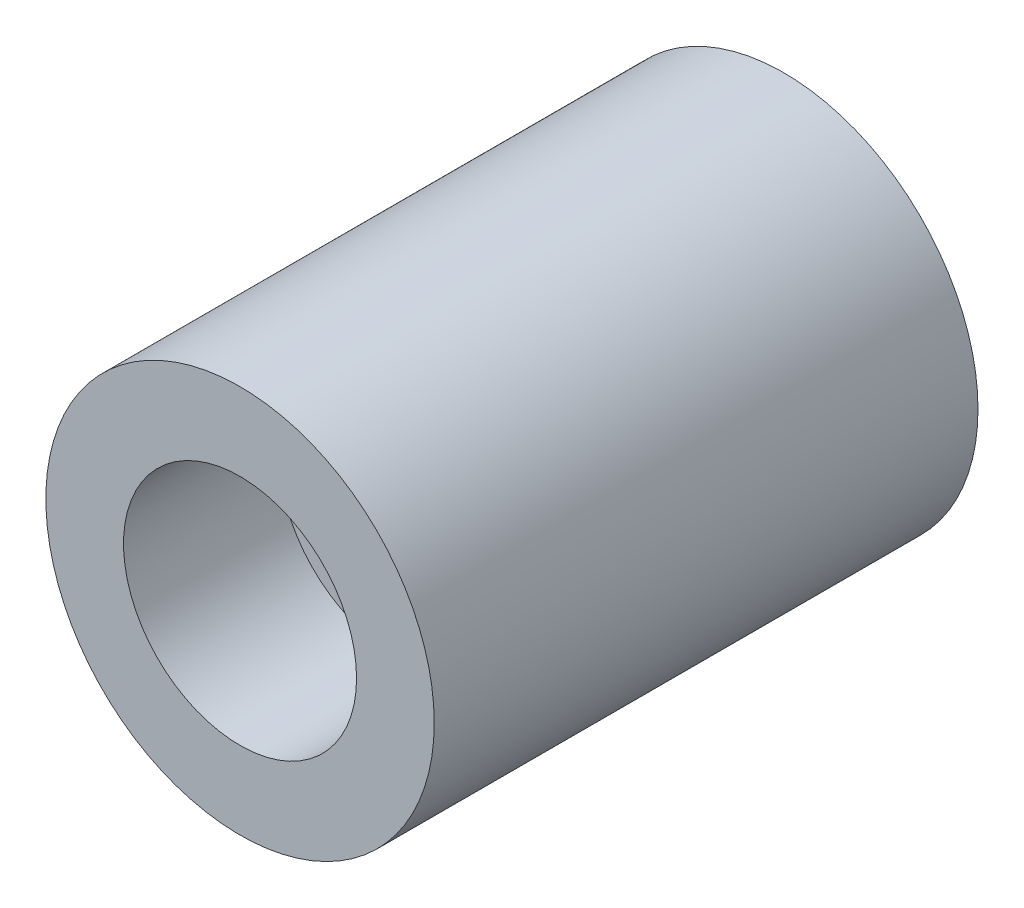
SolidWorks part; units mm, degrees
ref_plane "Front Plane" through (0, 0, 0) normal (0, 0, 1) x (1, 0, 0)
ref_plane "Top Plane" through (0, 0, 0) normal (0, 1, 0) x (1, 0, 0)
ref_plane "Right Plane" through (0, 0, 0) normal (1, 0, 0) x (0, 0, -1)
sketch "Sketch1" plane through (0, 0, 0) normal (0, 0, 1) x (1, 0, 0)
  circle A0 centre (0, 0) radius 50
  dimension "D1" = 100
extrude "Boss-Extrude1" add sketch "Sketch1" along normal blind 140
sketch "Sketch2" plane through (0, 0, 140) normal (0, 0, 1) x (1, 0, 0)
  circle A0 centre (0, 0) radius 30
  dimension "D1" = 60
extrude "Cut-Extrude1" cut sketch "Sketch2" against normal blind 40
sketch "Sketch4" plane through (0, 0, 140) normal (0, 0, 1) x (1, 0, 0)
  circle A0 centre (0, 0) radius 10
  dimension "D1" = 20
extrude "Cut-Extrude2" cut sketch "Sketch4" against normal blind 120
